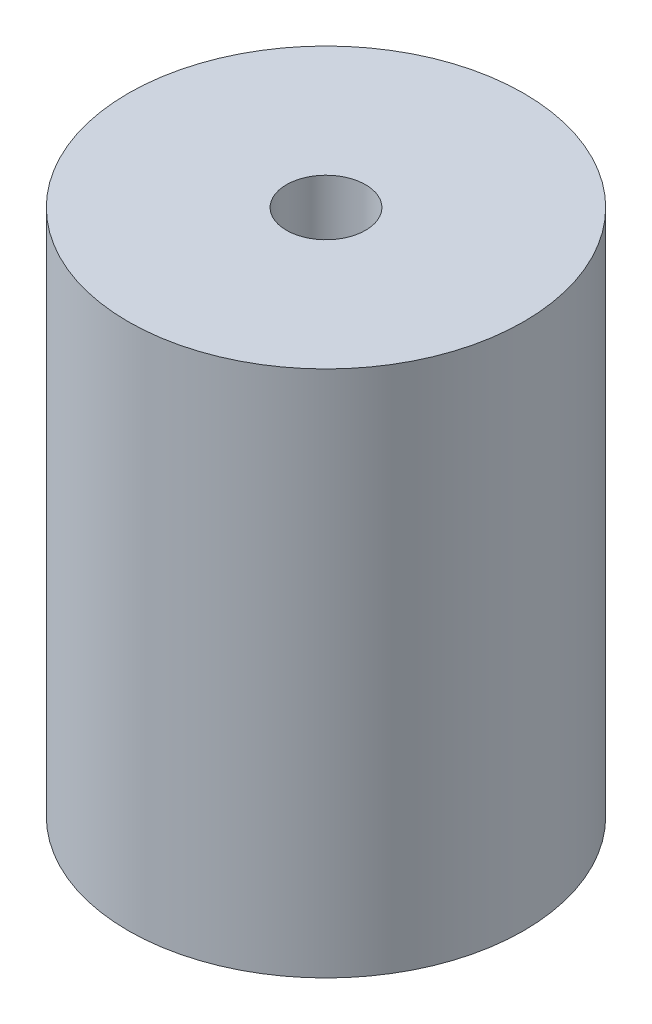
SolidWorks part; units mm, degrees
ref_plane "Front Plane" through (0, 0, 0) normal (0, 0, 1) x (1, 0, 0)
ref_plane "Top Plane" through (0, 0, 0) normal (0, 1, 0) x (1, 0, 0)
ref_plane "Right Plane" through (0, 0, 0) normal (1, 0, 0) x (0, 0, -1)
sketch "Sketch1" plane through (0, 0, 0) normal (0, 1, 0) x (1, 0, 0)
  circle A0 centre (0, 0) radius 15
extrude "Boss-Extrude1" add sketch "Sketch1" along normal blind 40
sketch "Sketch2" plane through (0, 40, 0) normal (0, 1, 0) x (1, 0, 0)
  circle A0 centre (0, 0) radius 3
extrude "Cut-Extrude1" cut sketch "Sketch2" against normal blind 20
sketch "Sketch3" plane through (0, 0, 0) normal (0, -1, 0) x (1, 0, 0)
  circle A0 centre (0, 0) radius 4
extrude "Cut-Extrude2" cut sketch "Sketch3" against normal blind 20
